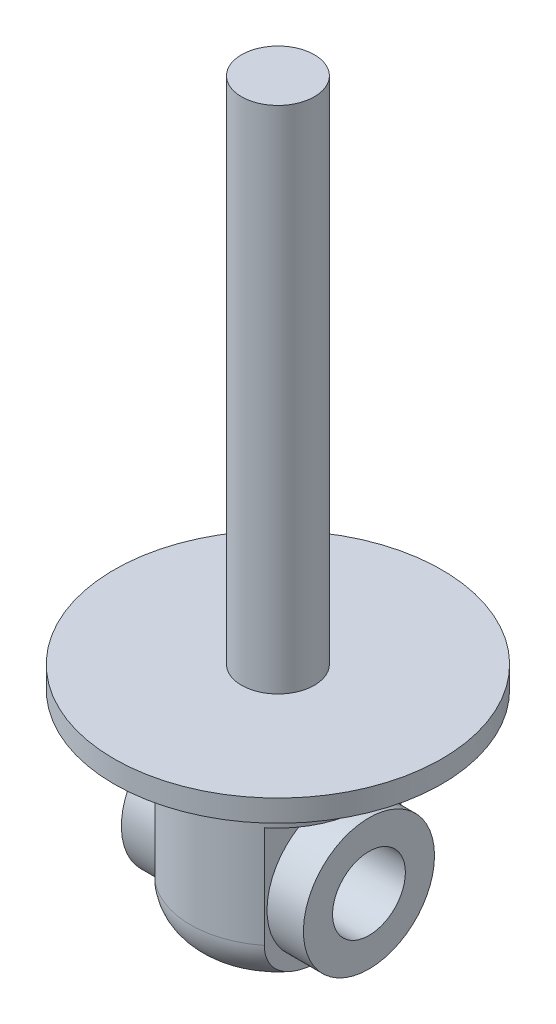
SolidWorks part; units mm, degrees
ref_plane "Front Plane" through (0, 0, 0) normal (0, 0, 1) x (1, 0, 0)
ref_plane "Top Plane" through (0, 0, 0) normal (0, 1, 0) x (1, 0, 0)
ref_plane "Right Plane" through (0, 0, 0) normal (1, 0, 0) x (0, 0, -1)
sketch "Sketch1" plane through (0, 0, 0) normal (0, 1, 0) x (1, 0, 0)
  circle A0 centre (0, 0) radius 22.5
extrude "Boss-Extrude1" add sketch "Sketch1" along normal blind 3
sketch "Sketch2" plane through (0, 3, 0) normal (0, 1, 0) x (1, 0, 0)
  circle A0 centre (0, 0) radius 5
extrude "Boss-Extrude2" add sketch "Sketch2" along normal blind 70
sketch "Sketch3" plane through (0, 0, 0) normal (0, -1, 0) x (1, 0, 0)
  circle A0 centre (0, 0) radius 12
extrude "Boss-Extrude3" add sketch "Sketch3" along normal blind 28
fillet "Fillet1" radius 6 1 edges at (0, -28, -12)
sketch "Sketch4" plane through (0, 0, 0) normal (0, 0, 1) x (1, 0, 0)
  line L0 (0, 0) -> (0, -28) construction
  line L1 (-6, -28) -> (6, -28) construction
  line L2 (7.5, -28) -> (27.5, -28)
  line L3 (27.5, -28) -> (27.5, -8)
  line L4 (27.5, -8) -> (7.5, -8)
  line L5 (7.5, -8) -> (7.5, -28)
  line L6 (-7.5, -8) -> (-7.5, -28)
  line L7 (-27.5, -8) -> (-7.5, -8)
  line L8 (-27.5, -28) -> (-27.5, -8)
  line L9 (-7.5, -28) -> (-27.5, -28)
  dimension "D1" = 15
  dimension "D2" = 20
  dimension "D3" = 20
extrude "Cut-Extrude1" cut sketch "Sketch4" against normal mid plane 28
sketch "Sketch6" plane through (7.5, 0, 0) normal (1, 0, 0) x (0, 0, -1)
  line L0 (0, 0) -> (0, -28) construction
  line L1 (-6, -28) -> (6, -28) construction
  circle A0 centre (0, -18) radius 5
  dimension "D1" = 10
extrude "Cut-Extrude2" cut sketch "Sketch6" against normal through all
sketch "Sketch7" plane through (0, 0, 0) normal (1, 0, 0) x (0, 0, -1)
  circle A0 centre (0, -18) radius 9
  circle A1 centre (0, -18) radius 5 construction
  circle A2 centre (0, -18) radius 5
extrude "Boss-Extrude4" add sketch "Sketch7" along normal mid plane 25
